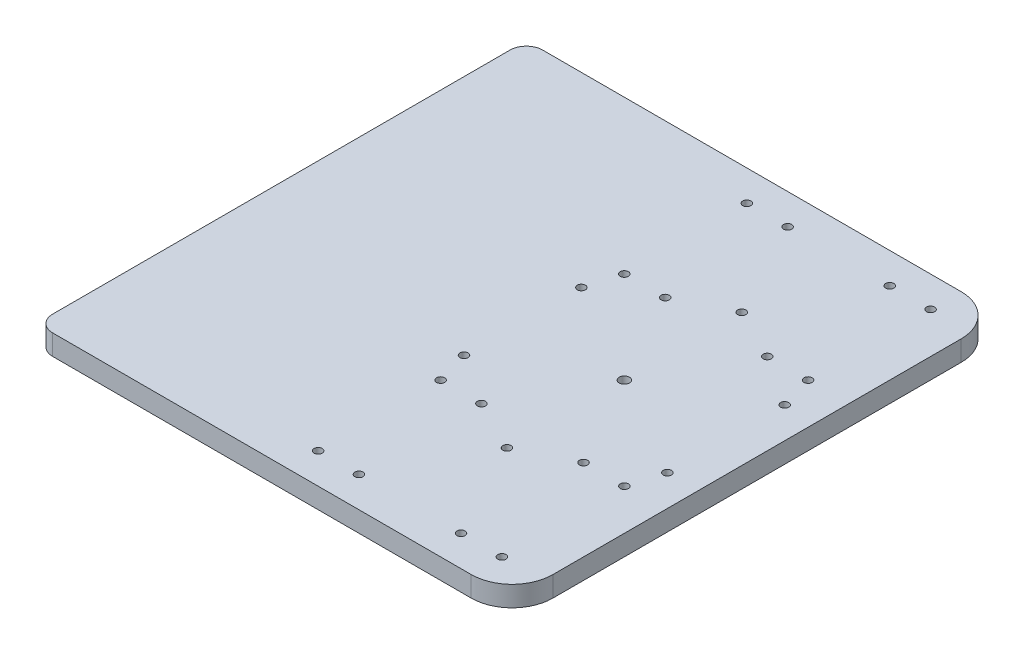
SolidWorks part; units mm, degrees
material "Acrylic (Medium-high impact)"
ref_plane "Front Plane" through (0, 0, 0) normal (0, 0, 1) x (1, 0, 0)
ref_plane "Top Plane" through (0, 0, 0) normal (0, 1, 0) x (1, 0, 0)
ref_plane "Right Plane" through (0, 0, 0) normal (1, 0, 0) x (0, 0, -1)
sketch "Sketch1" plane through (0, 0, 0) normal (0, 1, 0) x (1, 0, 0)
  line L0 (-193, 120) -> (45, 120)
  line L1 (65, 100) -> (65, -100)
  line L2 (45, -120) -> (-193, -120)
  line L3 (-213, -100) -> (-213, 100)
  line L4 (-288.3109, 0) -> (230.4751, 0) construction
  line L5 (0, -162.7992) -> (0, 177.1011) construction
  line L6 (-67.0966, 105) -> (59.4137, 105) construction
  line L7 (-50, 80) -> (50, 80) construction
  line L8 (-50, 80) -> (-50, 70) construction
  line L9 (-50, 70) -> (50, 70) construction
  line L10 (50, 80) -> (50, 70) construction
  line L11 (-50, 80) -> (50, 70) construction
  line L12 (-50, 70) -> (50, 80) construction
  line L13 (-72.1253, 45) -> (63.119, 45) construction
  line L14 (-45, 115.6016) -> (-45, 17.9398) construction
  line L15 (-25, 115.6016) -> (-25, 16.0872) construction
  line L16 (25, 115.6016) -> (25, 16.0872) construction
  line L17 (45, 112.6903) -> (45, 20.0572) construction
  circle A0 centre (0, 0) radius 67.5 construction
  arc A1 (-193, 120) -> (-213, 100) centre (-193, 100) ccw
  arc A2 (-193, -120) -> (-213, -100) centre (-193, -100) cw
  arc A3 (65, 100) -> (45, 120) centre (45, 100) ccw
  arc A4 (65, -100) -> (45, -120) centre (45, -100) cw
  circle A5 centre (0, 0) radius 57.5 construction
  circle A6 centre (0, -57.5) radius 2
  circle A7 centre (-49.7965, -28.75) radius 2
  circle A8 centre (-49.7965, 28.75) radius 2
  circle A9 centre (0, 57.5) radius 2
  circle A10 centre (49.7965, 28.75) radius 2
  circle A11 centre (49.7965, -28.75) radius 2
  circle A12 centre (0, 0) radius 2.5
  circle A13 centre (-45, 105) radius 2
  circle A14 centre (-25, 105) radius 2
  circle A15 centre (25, 105) radius 2
  circle A16 centre (45, 105) radius 2
  circle A17 centre (-45, 45) radius 2
  circle A18 centre (-25, 45) radius 2
  circle A19 centre (25, 45) radius 2
  circle A20 centre (45, 45) radius 2
  circle A21 centre (-45, -45) radius 2
  circle A22 centre (-25, -45) radius 2
  circle A23 centre (25, -45) radius 2
  circle A24 centre (45, -45) radius 2
  circle A25 centre (45, -105) radius 2
  circle A26 centre (25, -105) radius 2
  circle A27 centre (-25, -105) radius 2
  circle A28 centre (-45, -105) radius 2
  point P22 (0, 75)
  point P34 (0, 0)
  point P51 (50, 75)
  dimension "D1" = 135
  dimension "D6" = 20
  dimension "D7" = 20
  dimension "D8" = 20
  dimension "D9" = 20
  dimension "D10" = 115
  dimension "D11" = 4
  dimension "D13" = 5
  dimension "D23" = 4
  dimension "D24" = 4
  dimension "D25" = 4
  dimension "D26" = 4
  dimension "D27" = 4
  dimension "D28" = 4
  dimension "D29" = 4
  dimension "D30" = 4
  dimension "D2" = 120
  dimension "D3" = 120
  dimension "D4" = 65
  dimension "D5" = 213
  dimension "D14" = 100
  dimension "D15" = 10
  dimension "D16" = 70
  dimension "D17" = 5
  dimension "D18" = 5
  dimension "D19" = 20
  dimension "D20" = 20
  dimension "D21" = 25
  dimension "D22" = 25
  dimension "D12" = 6
extrude "Boss-Extrude1" add sketch "Sketch1" along normal blind 10
sketch "Sketch3" plane through (-213, 0, 0) normal (-1, 0, 0) x (0, 0, 1)
  line L1 (-120, 10) -> (120, 10)
  line L2 (-120, 10) -> (-120, 0)
  line L3 (-120, 0) -> (120, 0)
  line L4 (120, 10) -> (120, 0)
extrude "Cut-Extrude1" cut sketch "Sketch3" against normal blind 45
fillet "Fillet1" radius 8 2 edges at (-168, 5, -120) (-168, 5, 120)
